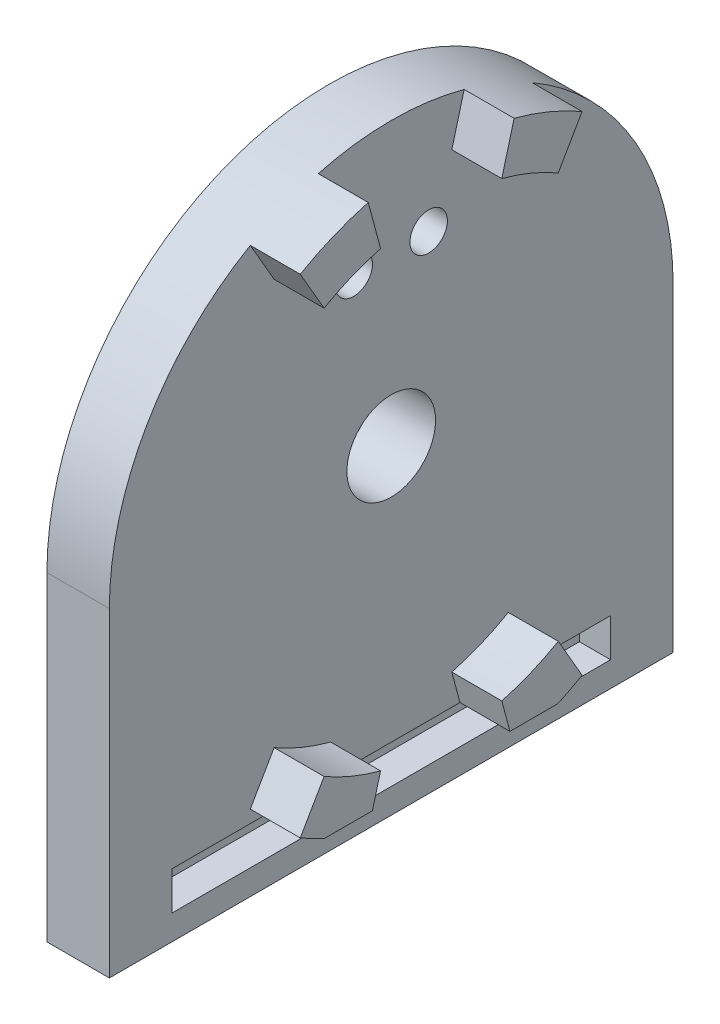
SolidWorks part; units mm, degrees
ref_plane "Front Plane" through (0, 0, 0) normal (0, 0, 1) x (1, 0, 0)
ref_plane "Top Plane" through (0, 0, 0) normal (0, 1, 0) x (1, 0, 0)
ref_plane "Right Plane" through (0, 0, 0) normal (1, 0, 0) x (0, 0, -1)
sketch "Sketch1" plane through (0, 0, 0) normal (1, 0, 0) x (0, 0, -1)
  circle A0 centre (0, 0) radius 22.568
extrude "Boss-Extrude1" add sketch "Sketch1" along normal blind 5
sketch "Sketch2" plane through (5, 0, 0) normal (1, 0, 0) x (0, 0, -1)
  line L0 (-22.568, 0) -> (-22.568, -25.616)
  line L1 (-22.568, -25.616) -> (22.568, -25.616)
  line L2 (22.568, -25.616) -> (22.568, 0)
  line L3 (22.568, 0) -> (-22.568, 0)
  circle A0 centre (0, 0) radius 22.568 construction
extrude "Boss-Extrude2" add sketch "Sketch2" against normal blind 5
sketch "Sketch3" plane through (5, 0, 0) normal (1, 0, 0) x (0, 0, -1)
  circle A0 centre (-3, 13.3712) radius 1.5
  circle A1 centre (3, 13.3712) radius 1.5
  circle A3 centre (0, 0) radius 3.55
extrude "Cut-Extrude1" cut sketch "Sketch3" against normal through all both and the other way through all
sketch "Sketch4" plane through (5, 0, 0) normal (1, 0, 0) x (0, 0, -1)
  line L0 (-22.568, 0) -> (-22.568, -25.616) construction
  line L1 (-17.568, -20.55) -> (17.568, -20.55)
  line L2 (-17.568, -20.55) -> (-17.568, -23.616)
  line L3 (-17.568, -23.616) -> (17.568, -23.616)
  line L4 (17.568, -20.55) -> (17.568, -23.616)
  line L5 (-22.568, -25.616) -> (22.568, -25.616) construction
  line L7 (22.568, -25.616) -> (22.568, 0) construction
  circle A0 centre (0, 0) radius 18.55 construction
  dimension "D1" = 5
  dimension "D2" = 5
  dimension "D3" = 2
  dimension "D4" = 2
extrude "Cut-Extrude2" cut sketch "Sketch4" against normal blind 2.5
sketch "Sketch5" plane through (5, 0, 0) normal (1, 0, 0) x (0, 0, -1)
  line L0 (0, 0) -> (-11.284, 19.5444)
  line L1 (0, 0) -> (-5.841, 21.799)
  line L2 (0, 0) -> (5.841, 21.799)
  line L3 (0, 0) -> (11.284, 19.5444)
  line L4 (0, 0) -> (-22.568, 0)
  line L5 (-22.568, 0) -> (22.568, 0) construction
  line L6 (0, 0) -> (11.284, -19.5444)
  line L7 (0, 0) -> (5.841, -21.799)
  line L8 (0, 0) -> (-5.841, -21.799)
  line L9 (0, 0) -> (-11.284, -19.5444)
  arc A0 (11.284, 19.5444) -> (5.841, 21.799) centre (0, 0) ccw
  arc A2 (9.375, 16.238) -> (4.8529, 18.1111) centre (0, 0) ccw
  arc A3 (-5.841, 21.799) -> (-11.284, 19.5444) centre (0, 0) ccw
  arc A4 (-4.8529, 18.1111) -> (-9.375, 16.238) centre (0, 0) ccw
  arc A5 (11.284, -19.5444) -> (5.841, -21.799) centre (0, 0) cw
  arc A6 (9.375, -16.238) -> (4.8529, -18.1111) centre (0, 0) cw
  arc A7 (-4.8529, -18.1111) -> (-9.375, -16.238) centre (0, 0) cw
  arc A8 (-5.841, -21.799) -> (-11.284, -19.5444) centre (0, 0) cw
  circle A9 centre (0, 0) radius 18.55 construction
  line M7 (-17.568, -20.55) -> (17.568, -20.55)
  arc M13 (22.568, 0) -> (-22.568, 0) centre (0, 0) ccw
  dimension "D1" = 0.2
  dimension "D2" = 30
  dimension "D3" = 15
  dimension "D4" = 15
  dimension "D5" = 60
extrude "Boss-Extrude3" add sketch "Sketch5" along normal blind 4 contours A4 L1 L0 M13 | A2 L3 L2 M13 | A8 L8 A7 L9 M7 | L6 A6 L7 A5 M7
